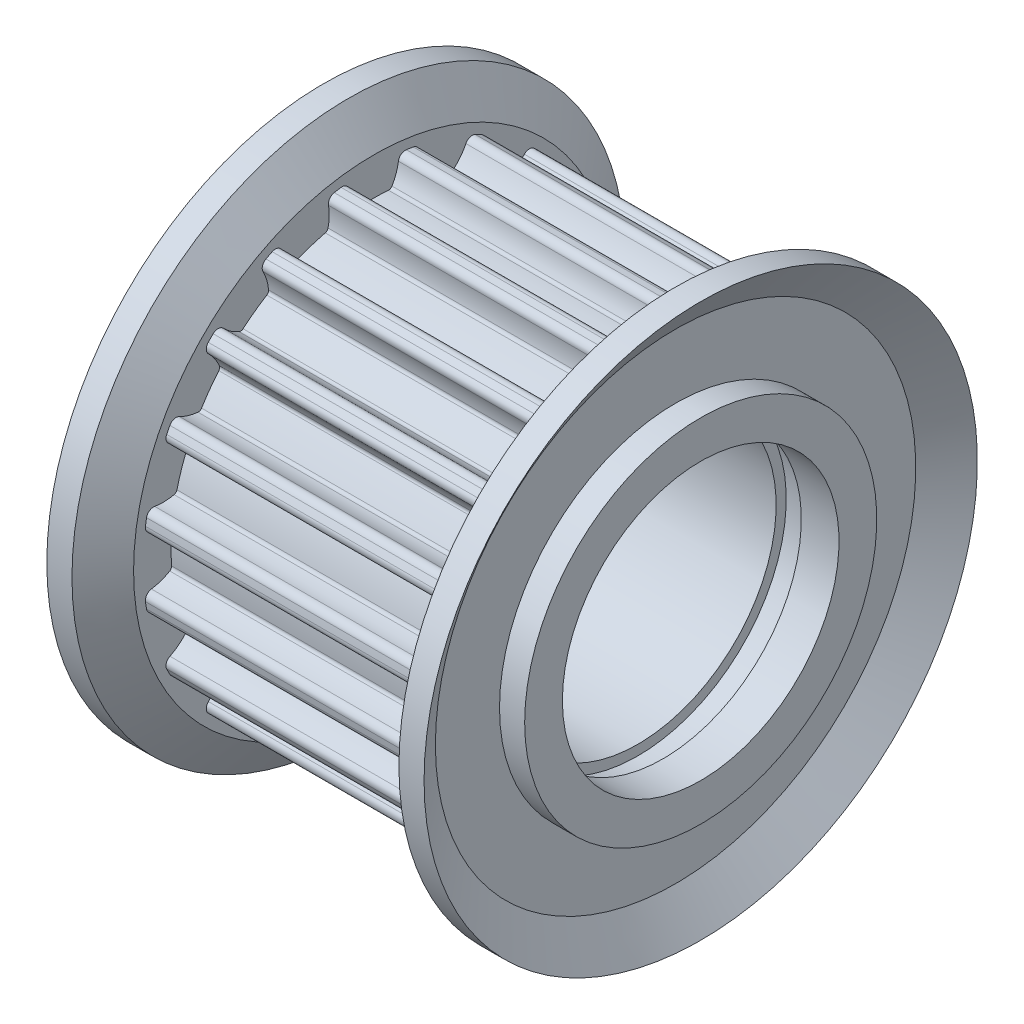
SolidWorks part; units mm, degrees
ref_plane "Front Plane" through (0, 0, 0) normal (0, 0, 1) x (1, 0, 0)
ref_plane "Top Plane" through (0, 0, 0) normal (0, 1, 0) x (1, 0, 0)
ref_plane "Right Plane" through (0, 0, 0) normal (1, 0, 0) x (0, 0, -1)
ref_plane "Plane1" through (0, 0, 0) normal (0, 0, 1) x (1, 0, 0)
sketch "Sketch1" plane through (0, 0, 0) normal (0, 0, 1) x (1, 0, 0)
  line L0 (-7.5, 4.5) -> (-5, 4.5)
  line L1 (-5, 4.5) -> (-5, 5.5)
  line L2 (-5, 5.5) -> (5, 5.5)
  line L3 (5, 5.5) -> (5, 5.9)
  line L4 (5, 5.9) -> (6, 5.9)
  line L5 (6, 5.9) -> (6, 5.5)
  line L6 (6, 5.5) -> (7.5, 5.5)
  line L7 (7.5, 5.5) -> (7.5, 7)
  line L8 (7.5, 7) -> (6.5, 7)
  line L9 (6.5, 7) -> (6.5, 9.55)
  line L10 (6.5, 9.55) -> (7.5, 11)
  line L11 (7.5, 11) -> (6.5, 11)
  line L12 (6.5, 11) -> (5.5, 9.55)
  line L13 (5.5, 9.55) -> (5.5, 9.17)
  line L14 (5.5, 9.17) -> (-5.5, 9.17)
  line L15 (-5.5, 9.17) -> (-5.5, 9.55)
  line L16 (-5.5, 9.55) -> (-6.5, 11)
  line L17 (-6.5, 11) -> (-7.5, 11)
  line L18 (-7.5, 11) -> (-6.5, 9.55)
  line L19 (-6.5, 9.55) -> (-6.5, 7)
  line L20 (-6.5, 7) -> (-7.5, 7)
  line L21 (-7.5, 7) -> (-7.5, 4.5)
  line L22 (20, 0) -> (-20, 0) construction
  dimension "D1" = 18.34
revolve "Revolve1" add sketch "Sketch1" angle 360 about L22
ref_plane "Plane2" through (5.5, 0, 0) normal (1, 0, 0) x (0, 0, -1)
sketch "Sketch2" plane through (5.5, 0, 0) normal (1, 0, 0) x (0, 0, -1)
  line L0 (1.2972, 9.0778) -> (1.2972, 9.8469)
  line L1 (-1.2972, 9.8469) -> (-1.2972, 9.0778)
  arc A0 (-1.2972, 9.0778) -> (-0.9803, 8.84) centre (-1.2575, 8.8006) cw
  arc A1 (-0.9803, 8.84) -> (-0.7246, 8.112) centre (0.975, 9.118) ccw
  arc A2 (-0.7246, 8.112) -> (-0.5846, 8.0388) centre (-0.5955, 8.1884) ccw
  arc A3 (-0.5846, 8.0388) -> (0.5846, 8.0388) centre (0, 0) cw
  arc A4 (0.5846, 8.0388) -> (0.7246, 8.112) centre (0.5955, 8.1884) ccw
  arc A5 (0.7246, 8.112) -> (0.9803, 8.84) centre (-0.975, 9.118) ccw
  arc A6 (0.9803, 8.84) -> (1.2972, 9.0778) centre (1.2575, 8.8006) cw
  arc A7 (1.2972, 9.8469) -> (-1.2972, 9.8469) centre (0, 0) ccw
extrude "Cut-Extrude1" cut sketch "Sketch2" against normal blind 11
ref_plane "Plane3" through (5.5, 0, 0) normal (1, 0, 0) x (0, 0, -1)
sketch "Sketch3" plane through (5.5, 0, 0) normal (1, 0, 0) x (0, 0, -1)
  line L0 (4.0389, 8.2326) -> (4.2765, 8.9641)
  line L1 (1.8092, 9.7658) -> (1.5715, 9.0343)
  arc A0 (1.5715, 9.0343) -> (1.7994, 8.7103) centre (1.5235, 8.7585) cw
  arc A1 (1.7994, 8.7103) -> (1.8176, 7.9388) centre (3.7449, 8.3705) ccw
  arc A2 (1.8176, 7.9388) -> (1.9281, 7.826) centre (1.964, 7.9716) ccw
  arc A3 (1.9281, 7.826) -> (3.0401, 7.4647) centre (0, 0) cw
  arc A4 (3.0401, 7.4647) -> (3.1958, 7.491) centre (3.0967, 7.6036) ccw
  arc A5 (3.1958, 7.491) -> (3.6641, 8.1044) centre (1.8903, 8.973) ccw
  arc A6 (3.6641, 8.1044) -> (4.0389, 8.2326) centre (3.9155, 7.9813) cw
  arc A7 (4.2765, 8.9641) -> (1.8092, 9.7658) centre (0, 0) ccw
extrude "Cut-Extrude2" cut sketch "Sketch3" against normal blind 11
ref_plane "Plane4" through (5.5, 0, 0) normal (1, 0, 0) x (0, 0, -1)
sketch "Sketch4" plane through (5.5, 0, 0) normal (1, 0, 0) x (0, 0, -1)
  line L0 (6.3852, 6.5816) -> (6.8373, 7.2039)
  line L1 (4.7385, 8.7288) -> (4.2864, 8.1065)
  arc A0 (4.2864, 8.1065) -> (4.4029, 7.728) centre (4.1555, 7.859) cw
  arc A1 (4.4029, 7.728) -> (4.1819, 6.9886) centre (6.1482, 6.8035) ccw
  arc A2 (4.1819, 6.9886) -> (4.2521, 6.8471) centre (4.3313, 6.9745) ccw
  arc A3 (4.2521, 6.8471) -> (5.198, 6.1599) centre (0, 0) cw
  arc A4 (5.198, 6.1599) -> (5.3543, 6.1368) centre (5.2948, 6.2745) ccw
  arc A5 (5.3543, 6.1368) -> (5.9891, 6.5755) centre (4.5706, 7.9497) ccw
  arc A6 (5.9891, 6.5755) -> (6.3852, 6.5816) centre (6.1902, 6.3807) cw
  arc A7 (6.8373, 7.2039) -> (4.7385, 8.7288) centre (0, 0) ccw
extrude "Cut-Extrude3" cut sketch "Sketch4" against normal blind 11
ref_plane "Plane5" through (5.5, 0, 0) normal (1, 0, 0) x (0, 0, -1)
sketch "Sketch5" plane through (5.5, 0, 0) normal (1, 0, 0) x (0, 0, -1)
  line L0 (8.1065, 4.2864) -> (8.7288, 4.7385)
  line L1 (7.2039, 6.8373) -> (6.5816, 6.3852)
  arc A0 (6.5816, 6.3852) -> (6.5755, 5.9891) centre (6.3807, 6.1902) cw
  arc A1 (6.5755, 5.9891) -> (6.1368, 5.3543) centre (7.9497, 4.5706) ccw
  arc A2 (6.1368, 5.3543) -> (6.1599, 5.198) centre (6.2745, 5.2948) ccw
  arc A3 (6.1599, 5.198) -> (6.8471, 4.2521) centre (0, 0) cw
  arc A4 (6.8471, 4.2521) -> (6.9886, 4.1819) centre (6.9745, 4.3313) ccw
  arc A5 (6.9886, 4.1819) -> (7.728, 4.4029) centre (6.8035, 6.1482) ccw
  arc A6 (7.728, 4.4029) -> (8.1065, 4.2864) centre (7.859, 4.1555) cw
  arc A7 (8.7288, 4.7385) -> (7.2039, 6.8373) centre (0, 0) ccw
extrude "Cut-Extrude4" cut sketch "Sketch5" against normal blind 11
ref_plane "Plane6" through (5.5, 0, 0) normal (1, 0, 0) x (0, 0, -1)
sketch "Sketch6" plane through (5.5, 0, 0) normal (1, 0, 0) x (0, 0, -1)
  line L0 (9.0343, 1.5715) -> (9.7658, 1.8092)
  line L1 (8.9641, 4.2765) -> (8.2326, 4.0389)
  arc A0 (8.2326, 4.0389) -> (8.1044, 3.6641) centre (7.9813, 3.9155) cw
  arc A1 (8.1044, 3.6641) -> (7.491, 3.1958) centre (8.973, 1.8903) ccw
  arc A2 (7.491, 3.1958) -> (7.4647, 3.0401) centre (7.6036, 3.0967) ccw
  arc A3 (7.4647, 3.0401) -> (7.826, 1.9281) centre (0, 0) cw
  arc A4 (7.826, 1.9281) -> (7.9388, 1.8176) centre (7.9716, 1.964) ccw
  arc A5 (7.9388, 1.8176) -> (8.7103, 1.7994) centre (8.3705, 3.7449) ccw
  arc A6 (8.7103, 1.7994) -> (9.0343, 1.5715) centre (8.7585, 1.5235) cw
  arc A7 (9.7658, 1.8092) -> (8.9641, 4.2765) centre (0, 0) ccw
extrude "Cut-Extrude5" cut sketch "Sketch6" against normal blind 11
ref_plane "Plane7" through (5.5, 0, 0) normal (1, 0, 0) x (0, 0, -1)
sketch "Sketch7" plane through (5.5, 0, 0) normal (1, 0, 0) x (0, 0, -1)
  line L0 (9.0778, -1.2972) -> (9.8469, -1.2972)
  line L1 (9.8469, 1.2972) -> (9.0778, 1.2972)
  arc A0 (9.0778, 1.2972) -> (8.84, 0.9803) centre (8.8006, 1.2575) cw
  arc A1 (8.84, 0.9803) -> (8.112, 0.7246) centre (9.118, -0.975) ccw
  arc A2 (8.112, 0.7246) -> (8.0388, 0.5846) centre (8.1884, 0.5955) ccw
  arc A3 (8.0388, 0.5846) -> (8.0388, -0.5846) centre (0, 0) cw
  arc A4 (8.0388, -0.5846) -> (8.112, -0.7246) centre (8.1884, -0.5955) ccw
  arc A5 (8.112, -0.7246) -> (8.84, -0.9803) centre (9.118, 0.975) ccw
  arc A6 (8.84, -0.9803) -> (9.0778, -1.2972) centre (8.8006, -1.2575) cw
  arc A7 (9.8469, -1.2972) -> (9.8469, 1.2972) centre (0, 0) ccw
extrude "Cut-Extrude6" cut sketch "Sketch7" against normal blind 11
ref_plane "Plane8" through (5.5, 0, 0) normal (1, 0, 0) x (0, 0, -1)
sketch "Sketch8" plane through (5.5, 0, 0) normal (1, 0, 0) x (0, 0, -1)
  line L0 (8.2326, -4.0389) -> (8.9641, -4.2765)
  line L1 (9.7658, -1.8092) -> (9.0343, -1.5715)
  arc A0 (9.0343, -1.5715) -> (8.7103, -1.7994) centre (8.7585, -1.5235) cw
  arc A1 (8.7103, -1.7994) -> (7.9388, -1.8176) centre (8.3705, -3.7449) ccw
  arc A2 (7.9388, -1.8176) -> (7.826, -1.9281) centre (7.9716, -1.964) ccw
  arc A3 (7.826, -1.9281) -> (7.4647, -3.0401) centre (0, 0) cw
  arc A4 (7.4647, -3.0401) -> (7.491, -3.1958) centre (7.6036, -3.0967) ccw
  arc A5 (7.491, -3.1958) -> (8.1044, -3.6641) centre (8.973, -1.8903) ccw
  arc A6 (8.1044, -3.6641) -> (8.2326, -4.0389) centre (7.9813, -3.9155) cw
  arc A7 (8.9641, -4.2765) -> (9.7658, -1.8092) centre (0, 0) ccw
extrude "Cut-Extrude7" cut sketch "Sketch8" against normal blind 11
ref_plane "Plane9" through (5.5, 0, 0) normal (1, 0, 0) x (0, 0, -1)
sketch "Sketch9" plane through (5.5, 0, 0) normal (1, 0, 0) x (0, 0, -1)
  line L0 (6.5816, -6.3852) -> (7.2039, -6.8373)
  line L1 (8.7288, -4.7385) -> (8.1065, -4.2864)
  arc A0 (8.1065, -4.2864) -> (7.728, -4.4029) centre (7.859, -4.1555) cw
  arc A1 (7.728, -4.4029) -> (6.9886, -4.1819) centre (6.8035, -6.1482) ccw
  arc A2 (6.9886, -4.1819) -> (6.8471, -4.2521) centre (6.9745, -4.3313) ccw
  arc A3 (6.8471, -4.2521) -> (6.1599, -5.198) centre (0, 0) cw
  arc A4 (6.1599, -5.198) -> (6.1368, -5.3543) centre (6.2745, -5.2948) ccw
  arc A5 (6.1368, -5.3543) -> (6.5755, -5.9891) centre (7.9497, -4.5706) ccw
  arc A6 (6.5755, -5.9891) -> (6.5816, -6.3852) centre (6.3807, -6.1902) cw
  arc A7 (7.2039, -6.8373) -> (8.7288, -4.7385) centre (0, 0) ccw
extrude "Cut-Extrude8" cut sketch "Sketch9" against normal blind 11
ref_plane "Plane10" through (5.5, 0, 0) normal (1, 0, 0) x (0, 0, -1)
sketch "Sketch10" plane through (5.5, 0, 0) normal (1, 0, 0) x (0, 0, -1)
  line L0 (4.2864, -8.1065) -> (4.7385, -8.7288)
  line L1 (6.8373, -7.2039) -> (6.3852, -6.5816)
  arc A0 (6.3852, -6.5816) -> (5.9891, -6.5755) centre (6.1902, -6.3807) cw
  arc A1 (5.9891, -6.5755) -> (5.3543, -6.1368) centre (4.5706, -7.9497) ccw
  arc A2 (5.3543, -6.1368) -> (5.198, -6.1599) centre (5.2948, -6.2745) ccw
  arc A3 (5.198, -6.1599) -> (4.2521, -6.8471) centre (0, 0) cw
  arc A4 (4.2521, -6.8471) -> (4.1819, -6.9886) centre (4.3313, -6.9745) ccw
  arc A5 (4.1819, -6.9886) -> (4.4029, -7.728) centre (6.1482, -6.8035) ccw
  arc A6 (4.4029, -7.728) -> (4.2864, -8.1065) centre (4.1555, -7.859) cw
  arc A7 (4.7385, -8.7288) -> (6.8373, -7.2039) centre (0, 0) ccw
extrude "Cut-Extrude9" cut sketch "Sketch10" against normal blind 11
ref_plane "Plane11" through (5.5, 0, 0) normal (1, 0, 0) x (0, 0, -1)
sketch "Sketch11" plane through (5.5, 0, 0) normal (1, 0, 0) x (0, 0, -1)
  line L0 (1.5715, -9.0343) -> (1.8092, -9.7658)
  line L1 (4.2765, -8.9641) -> (4.0389, -8.2326)
  arc A0 (4.0389, -8.2326) -> (3.6641, -8.1044) centre (3.9155, -7.9813) cw
  arc A1 (3.6641, -8.1044) -> (3.1958, -7.491) centre (1.8903, -8.973) ccw
  arc A2 (3.1958, -7.491) -> (3.0401, -7.4647) centre (3.0967, -7.6036) ccw
  arc A3 (3.0401, -7.4647) -> (1.9281, -7.826) centre (0, 0) cw
  arc A4 (1.9281, -7.826) -> (1.8176, -7.9388) centre (1.964, -7.9716) ccw
  arc A5 (1.8176, -7.9388) -> (1.7994, -8.7103) centre (3.7449, -8.3705) ccw
  arc A6 (1.7994, -8.7103) -> (1.5715, -9.0343) centre (1.5235, -8.7585) cw
  arc A7 (1.8092, -9.7658) -> (4.2765, -8.9641) centre (0, 0) ccw
extrude "Cut-Extrude10" cut sketch "Sketch11" against normal blind 11
ref_plane "Plane12" through (5.5, 0, 0) normal (1, 0, 0) x (0, 0, -1)
sketch "Sketch12" plane through (5.5, 0, 0) normal (1, 0, 0) x (0, 0, -1)
  line L0 (-1.2972, -9.0778) -> (-1.2972, -9.8469)
  line L1 (1.2972, -9.8469) -> (1.2972, -9.0778)
  arc A0 (1.2972, -9.0778) -> (0.9803, -8.84) centre (1.2575, -8.8006) cw
  arc A1 (0.9803, -8.84) -> (0.7246, -8.112) centre (-0.975, -9.118) ccw
  arc A2 (0.7246, -8.112) -> (0.5846, -8.0388) centre (0.5955, -8.1884) ccw
  arc A3 (0.5846, -8.0388) -> (-0.5846, -8.0388) centre (0, 0) cw
  arc A4 (-0.5846, -8.0388) -> (-0.7246, -8.112) centre (-0.5955, -8.1884) ccw
  arc A5 (-0.7246, -8.112) -> (-0.9803, -8.84) centre (0.975, -9.118) ccw
  arc A6 (-0.9803, -8.84) -> (-1.2972, -9.0778) centre (-1.2575, -8.8006) cw
  arc A7 (-1.2972, -9.8469) -> (1.2972, -9.8469) centre (0, 0) ccw
extrude "Cut-Extrude11" cut sketch "Sketch12" against normal blind 11
ref_plane "Plane13" through (5.5, 0, 0) normal (1, 0, 0) x (0, 0, -1)
sketch "Sketch13" plane through (5.5, 0, 0) normal (1, 0, 0) x (0, 0, -1)
  line L0 (-4.0389, -8.2326) -> (-4.2765, -8.9641)
  line L1 (-1.8092, -9.7658) -> (-1.5715, -9.0343)
  arc A0 (-1.5715, -9.0343) -> (-1.7994, -8.7103) centre (-1.5235, -8.7585) cw
  arc A1 (-1.7994, -8.7103) -> (-1.8176, -7.9388) centre (-3.7449, -8.3705) ccw
  arc A2 (-1.8176, -7.9388) -> (-1.9281, -7.826) centre (-1.964, -7.9716) ccw
  arc A3 (-1.9281, -7.826) -> (-3.0401, -7.4647) centre (0, 0) cw
  arc A4 (-3.0401, -7.4647) -> (-3.1958, -7.491) centre (-3.0967, -7.6036) ccw
  arc A5 (-3.1958, -7.491) -> (-3.6641, -8.1044) centre (-1.8903, -8.973) ccw
  arc A6 (-3.6641, -8.1044) -> (-4.0389, -8.2326) centre (-3.9155, -7.9813) cw
  arc A7 (-4.2765, -8.9641) -> (-1.8092, -9.7658) centre (0, 0) ccw
extrude "Cut-Extrude12" cut sketch "Sketch13" against normal blind 11
ref_plane "Plane14" through (5.5, 0, 0) normal (1, 0, 0) x (0, 0, -1)
sketch "Sketch14" plane through (5.5, 0, 0) normal (1, 0, 0) x (0, 0, -1)
  line L0 (-6.3852, -6.5816) -> (-6.8373, -7.2039)
  line L1 (-4.7385, -8.7288) -> (-4.2864, -8.1065)
  arc A0 (-4.2864, -8.1065) -> (-4.4029, -7.728) centre (-4.1555, -7.859) cw
  arc A1 (-4.4029, -7.728) -> (-4.1819, -6.9886) centre (-6.1482, -6.8035) ccw
  arc A2 (-4.1819, -6.9886) -> (-4.2521, -6.8471) centre (-4.3313, -6.9745) ccw
  arc A3 (-4.2521, -6.8471) -> (-5.198, -6.1599) centre (0, 0) cw
  arc A4 (-5.198, -6.1599) -> (-5.3543, -6.1368) centre (-5.2948, -6.2745) ccw
  arc A5 (-5.3543, -6.1368) -> (-5.9891, -6.5755) centre (-4.5706, -7.9497) ccw
  arc A6 (-5.9891, -6.5755) -> (-6.3852, -6.5816) centre (-6.1902, -6.3807) cw
  arc A7 (-6.8373, -7.2039) -> (-4.7385, -8.7288) centre (0, 0) ccw
extrude "Cut-Extrude13" cut sketch "Sketch14" against normal blind 11
ref_plane "Plane15" through (5.5, 0, 0) normal (1, 0, 0) x (0, 0, -1)
sketch "Sketch15" plane through (5.5, 0, 0) normal (1, 0, 0) x (0, 0, -1)
  line L0 (-8.1065, -4.2864) -> (-8.7288, -4.7385)
  line L1 (-7.2039, -6.8373) -> (-6.5816, -6.3852)
  arc A0 (-6.5816, -6.3852) -> (-6.5755, -5.9891) centre (-6.3807, -6.1902) cw
  arc A1 (-6.5755, -5.9891) -> (-6.1368, -5.3543) centre (-7.9497, -4.5706) ccw
  arc A2 (-6.1368, -5.3543) -> (-6.1599, -5.198) centre (-6.2745, -5.2948) ccw
  arc A3 (-6.1599, -5.198) -> (-6.8471, -4.2521) centre (0, 0) cw
  arc A4 (-6.8471, -4.2521) -> (-6.9886, -4.1819) centre (-6.9745, -4.3313) ccw
  arc A5 (-6.9886, -4.1819) -> (-7.728, -4.4029) centre (-6.8035, -6.1482) ccw
  arc A6 (-7.728, -4.4029) -> (-8.1065, -4.2864) centre (-7.859, -4.1555) cw
  arc A7 (-8.7288, -4.7385) -> (-7.2039, -6.8373) centre (0, 0) ccw
extrude "Cut-Extrude14" cut sketch "Sketch15" against normal blind 11
ref_plane "Plane16" through (5.5, 0, 0) normal (1, 0, 0) x (0, 0, -1)
sketch "Sketch16" plane through (5.5, 0, 0) normal (1, 0, 0) x (0, 0, -1)
  line L0 (-9.0343, -1.5715) -> (-9.7658, -1.8092)
  line L1 (-8.9641, -4.2765) -> (-8.2326, -4.0389)
  arc A0 (-8.2326, -4.0389) -> (-8.1044, -3.6641) centre (-7.9813, -3.9155) cw
  arc A1 (-8.1044, -3.6641) -> (-7.491, -3.1958) centre (-8.973, -1.8903) ccw
  arc A2 (-7.491, -3.1958) -> (-7.4647, -3.0401) centre (-7.6036, -3.0967) ccw
  arc A3 (-7.4647, -3.0401) -> (-7.826, -1.9281) centre (0, 0) cw
  arc A4 (-7.826, -1.9281) -> (-7.9388, -1.8176) centre (-7.9716, -1.964) ccw
  arc A5 (-7.9388, -1.8176) -> (-8.7103, -1.7994) centre (-8.3705, -3.7449) ccw
  arc A6 (-8.7103, -1.7994) -> (-9.0343, -1.5715) centre (-8.7585, -1.5235) cw
  arc A7 (-9.7658, -1.8092) -> (-8.9641, -4.2765) centre (0, 0) ccw
extrude "Cut-Extrude15" cut sketch "Sketch16" against normal blind 11
ref_plane "Plane17" through (5.5, 0, 0) normal (1, 0, 0) x (0, 0, -1)
sketch "Sketch17" plane through (5.5, 0, 0) normal (1, 0, 0) x (0, 0, -1)
  line L0 (-9.0778, 1.2972) -> (-9.8469, 1.2972)
  line L1 (-9.8469, -1.2972) -> (-9.0778, -1.2972)
  arc A0 (-9.0778, -1.2972) -> (-8.84, -0.9803) centre (-8.8006, -1.2575) cw
  arc A1 (-8.84, -0.9803) -> (-8.112, -0.7246) centre (-9.118, 0.975) ccw
  arc A2 (-8.112, -0.7246) -> (-8.0388, -0.5846) centre (-8.1884, -0.5955) ccw
  arc A3 (-8.0388, -0.5846) -> (-8.0388, 0.5846) centre (0, 0) cw
  arc A4 (-8.0388, 0.5846) -> (-8.112, 0.7246) centre (-8.1884, 0.5955) ccw
  arc A5 (-8.112, 0.7246) -> (-8.84, 0.9803) centre (-9.118, -0.975) ccw
  arc A6 (-8.84, 0.9803) -> (-9.0778, 1.2972) centre (-8.8006, 1.2575) cw
  arc A7 (-9.8469, 1.2972) -> (-9.8469, -1.2972) centre (0, 0) ccw
extrude "Cut-Extrude16" cut sketch "Sketch17" against normal blind 11
ref_plane "Plane18" through (5.5, 0, 0) normal (1, 0, 0) x (0, 0, -1)
sketch "Sketch18" plane through (5.5, 0, 0) normal (1, 0, 0) x (0, 0, -1)
  line L0 (-8.2326, 4.0389) -> (-8.9641, 4.2765)
  line L1 (-9.7658, 1.8092) -> (-9.0343, 1.5715)
  arc A0 (-9.0343, 1.5715) -> (-8.7103, 1.7994) centre (-8.7585, 1.5235) cw
  arc A1 (-8.7103, 1.7994) -> (-7.9388, 1.8176) centre (-8.3705, 3.7449) ccw
  arc A2 (-7.9388, 1.8176) -> (-7.826, 1.9281) centre (-7.9716, 1.964) ccw
  arc A3 (-7.826, 1.9281) -> (-7.4647, 3.0401) centre (0, 0) cw
  arc A4 (-7.4647, 3.0401) -> (-7.491, 3.1958) centre (-7.6036, 3.0967) ccw
  arc A5 (-7.491, 3.1958) -> (-8.1044, 3.6641) centre (-8.973, 1.8903) ccw
  arc A6 (-8.1044, 3.6641) -> (-8.2326, 4.0389) centre (-7.9813, 3.9155) cw
  arc A7 (-8.9641, 4.2765) -> (-9.7658, 1.8092) centre (0, 0) ccw
extrude "Cut-Extrude17" cut sketch "Sketch18" against normal blind 11
ref_plane "Plane19" through (5.5, 0, 0) normal (1, 0, 0) x (0, 0, -1)
sketch "Sketch19" plane through (5.5, 0, 0) normal (1, 0, 0) x (0, 0, -1)
  line L0 (-6.5816, 6.3852) -> (-7.2039, 6.8373)
  line L1 (-8.7288, 4.7385) -> (-8.1065, 4.2864)
  arc A0 (-8.1065, 4.2864) -> (-7.728, 4.4029) centre (-7.859, 4.1555) cw
  arc A1 (-7.728, 4.4029) -> (-6.9886, 4.1819) centre (-6.8035, 6.1482) ccw
  arc A2 (-6.9886, 4.1819) -> (-6.8471, 4.2521) centre (-6.9745, 4.3313) ccw
  arc A3 (-6.8471, 4.2521) -> (-6.1599, 5.198) centre (0, 0) cw
  arc A4 (-6.1599, 5.198) -> (-6.1368, 5.3543) centre (-6.2745, 5.2948) ccw
  arc A5 (-6.1368, 5.3543) -> (-6.5755, 5.9891) centre (-7.9497, 4.5706) ccw
  arc A6 (-6.5755, 5.9891) -> (-6.5816, 6.3852) centre (-6.3807, 6.1902) cw
  arc A7 (-7.2039, 6.8373) -> (-8.7288, 4.7385) centre (0, 0) ccw
extrude "Cut-Extrude18" cut sketch "Sketch19" against normal blind 11
ref_plane "Plane20" through (5.5, 0, 0) normal (1, 0, 0) x (0, 0, -1)
sketch "Sketch20" plane through (5.5, 0, 0) normal (1, 0, 0) x (0, 0, -1)
  line L0 (-4.2864, 8.1065) -> (-4.7385, 8.7288)
  line L1 (-6.8373, 7.2039) -> (-6.3852, 6.5816)
  arc A0 (-6.3852, 6.5816) -> (-5.9891, 6.5755) centre (-6.1902, 6.3807) cw
  arc A1 (-5.9891, 6.5755) -> (-5.3543, 6.1368) centre (-4.5706, 7.9497) ccw
  arc A2 (-5.3543, 6.1368) -> (-5.198, 6.1599) centre (-5.2948, 6.2745) ccw
  arc A3 (-5.198, 6.1599) -> (-4.2521, 6.8471) centre (0, 0) cw
  arc A4 (-4.2521, 6.8471) -> (-4.1819, 6.9886) centre (-4.3313, 6.9745) ccw
  arc A5 (-4.1819, 6.9886) -> (-4.4029, 7.728) centre (-6.1482, 6.8035) ccw
  arc A6 (-4.4029, 7.728) -> (-4.2864, 8.1065) centre (-4.1555, 7.859) cw
  arc A7 (-4.7385, 8.7288) -> (-6.8373, 7.2039) centre (0, 0) ccw
extrude "Cut-Extrude19" cut sketch "Sketch20" against normal blind 11
ref_plane "Plane21" through (5.5, 0, 0) normal (1, 0, 0) x (0, 0, -1)
sketch "Sketch21" plane through (5.5, 0, 0) normal (1, 0, 0) x (0, 0, -1)
  line L0 (-1.5715, 9.0343) -> (-1.8092, 9.7658)
  line L1 (-4.2765, 8.9641) -> (-4.0389, 8.2326)
  arc A0 (-4.0389, 8.2326) -> (-3.6641, 8.1044) centre (-3.9155, 7.9813) cw
  arc A1 (-3.6641, 8.1044) -> (-3.1958, 7.491) centre (-1.8903, 8.973) ccw
  arc A2 (-3.1958, 7.491) -> (-3.0401, 7.4647) centre (-3.0967, 7.6036) ccw
  arc A3 (-3.0401, 7.4647) -> (-1.9281, 7.826) centre (0, 0) cw
  arc A4 (-1.9281, 7.826) -> (-1.8176, 7.9388) centre (-1.964, 7.9716) ccw
  arc A5 (-1.8176, 7.9388) -> (-1.7994, 8.7103) centre (-3.7449, 8.3705) ccw
  arc A6 (-1.7994, 8.7103) -> (-1.5715, 9.0343) centre (-1.5235, 8.7585) cw
  arc A7 (-1.8092, 9.7658) -> (-4.2765, 8.9641) centre (0, 0) ccw
extrude "Cut-Extrude20" cut sketch "Sketch21" against normal blind 11
sketch "Sketch23" plane through (-7.5, 0, 0) normal (-1, 0, 0) x (0, 0, 1)
  circle A0 centre (0, 0) radius 5
  dimension "D1" = 10
extrude "Cut-Extrude21" cut sketch "Sketch23" against normal through all
sketch "Sketch24" plane through (0, 0, 0) normal (0, 1, 0) x (1, 0, 0)
  circle A0 centre (0, 0) radius 0.75
  dimension "D1" = 1.5
extrude "Cut-Extrude22" cut sketch "Sketch24" against normal through all
